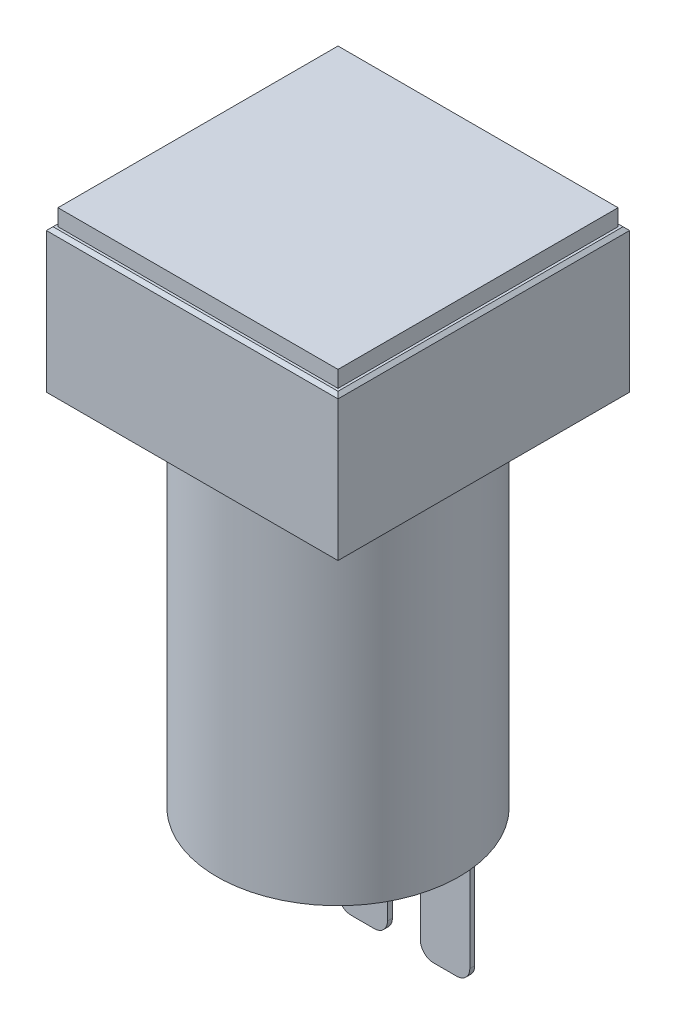
SolidWorks part; units mm, degrees
ref_plane "前视基准面" through (0, 0, 0) normal (0, 0, 1) x (1, 0, 0)
ref_plane "上视基准面" through (0, 0, 0) normal (0, 1, 0) x (1, 0, 0)
ref_plane "右视基准面" through (0, 0, 0) normal (1, 0, 0) x (0, 0, -1)
sketch "草图1" plane through (0, 0, 0) normal (0, 1, 0) x (1, 0, 0)
  line L1 (-8.85, 8.85) -> (8.85, 8.85)
  line L2 (-8.85, 8.85) -> (-8.85, -8.85)
  line L3 (-8.85, -8.85) -> (8.85, -8.85)
  line L4 (8.85, 8.85) -> (8.85, -8.85)
  line L5 (-8.85, 8.85) -> (8.85, -8.85) construction
  line L6 (-8.85, -8.85) -> (8.85, 8.85) construction
  point P0 (0, 0)
  dimension "D1" = 17.7
  dimension "D2" = 17.7
extrude "凸台-拉伸1" add sketch "草图1" along normal blind 8.7
sketch "草图2" plane through (0, 0, 0) normal (0, -1, 0) x (1, 0, 0)
  circle A0 centre (0, 0) radius 7.35
  dimension "D1" = 14.7
extrude "凸台-拉伸2" add sketch "草图2" along normal blind 21.8
sketch "草图3" plane through (0, -21.8, 0) normal (0, -1, 0) x (1, 0, 0)
  line L0 (0, 0) -> (0, -1.5) construction
  line L1 (-6.5, -1.5) -> (-3.5, -1.5)
  line L2 (-6.5, -1.5) -> (-6.5, -1.8)
  line L3 (-6.5, -1.8) -> (-3.5, -1.8)
  line L4 (-3.5, -1.5) -> (-3.5, -1.8)
  line L5 (-1.5, -1.8) -> (1.5, -1.8)
  line L6 (-1.5, -1.8) -> (-1.5, -1.5)
  line L7 (-1.5, -1.5) -> (1.5, -1.5)
  line L8 (1.5, -1.8) -> (1.5, -1.5)
  line L9 (3.5, -1.5) -> (6.5, -1.5)
  line L10 (3.5, -1.5) -> (3.5, -1.8)
  line L11 (3.5, -1.8) -> (6.5, -1.8)
  line L12 (6.5, -1.5) -> (6.5, -1.8)
  point P15 (-1.5, -1.65)
  point P16 (1.5, -1.65)
  dimension "D1" = 3
  dimension "D2" = 3
  dimension "D3" = 3
  dimension "D4" = 0.3
  dimension "D5" = 0.3
  dimension "D6" = 0.3
  dimension "D7" = 1.5
  dimension "D8" = 2
  dimension "D9" = 2
extrude "凸台-拉伸3" add sketch "草图3" along normal blind 6.8
fillet "圆角1" radius 0.8 6 edges at (6.5, -28.6, -1.65) (3.5, -28.6, -1.65) (1.5, -28.6, -1.65) (-1.5, -28.6, -1.65) (-3.5, -28.6, -1.65) (-6.5, -28.6, -1.65)
sketch "草图4" plane through (0, 8.7, 0) normal (0, 1, 0) x (1, 0, 0)
  line L1 (-8.5, 8.5) -> (8.5, 8.5)
  line L2 (-8.5, 8.5) -> (-8.5, -8.5)
  line L3 (-8.5, -8.5) -> (8.5, -8.5)
  line L4 (8.5, 8.5) -> (8.5, -8.5)
  line L5 (-8.5, 8.5) -> (8.5, -8.5) construction
  line L6 (-8.5, -8.5) -> (8.5, 8.5) construction
  point P0 (0, 0)
  dimension "D1" = 17
  dimension "D2" = 17
extrude "凸台-拉伸4" add sketch "草图4" along normal blind 1
chamfer "倒角1" distance 0.2 angle 45 4 edges at (0, 8.7, 8.85) (8.85, 8.7, 0) (0, 8.7, -8.85) (-8.85, 8.7, 0)
